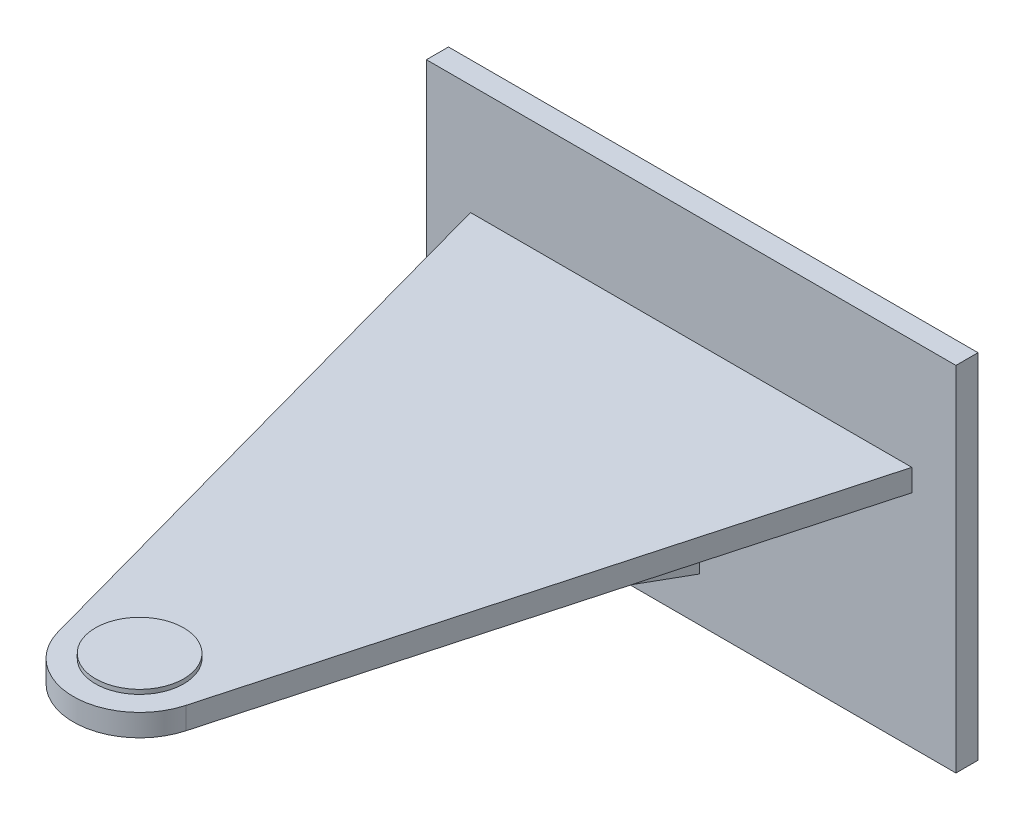
SolidWorks part; units mm, degrees
ref_plane "Frontal" through (0, 0, 0) normal (0, 0, 1) x (1, 0, 0)
ref_plane "Horizontal" through (0, 0, 0) normal (0, 1, 0) x (1, 0, 0)
ref_plane "Profile" through (0, 0, 0) normal (1, 0, 0) x (0, 0, -1)
sketch "Sketch1" plane through (0, 0, 0) normal (0, 0, 1) x (1, 0, 0)
  line L0 (-76.2, 50.8) -> (76.2, -50.8) construction
  line L1 (-76.2, 50.8) -> (76.2, 50.8)
  line L2 (-76.2, 50.8) -> (-76.2, -50.8)
  line L3 (-76.2, -50.8) -> (76.2, -50.8)
  line L4 (76.2, 50.8) -> (76.2, -50.8)
  dimension "D1" = 152.4
  dimension "D2" = 101.6
extrude "Extrude1" add sketch "Sketch1" along normal blind 6.35
ref_plane "Plane1" through (0, 19.05, 0) normal (0, 1, 0) x (-1, 0, 0)
sketch "Sketch3" plane through (0, 19.05, 0) normal (0, 1, 0) x (-1, 0, 0)
  line L0 (0, 0) -> (0, 69.344) construction
  line L1 (63.5, 6.35) -> (18.3656, 170.1603)
  line L2 (-63.5, 6.35) -> (-18.3656, 170.1603)
  line L3 (-76.2, 6.35) -> (76.2, 6.35) construction
  line L4 (63.5, 6.35) -> (-63.5, 6.35)
  arc A0 (18.3656, 170.1603) -> (0, 184.15) centre (0, 165.1) ccw
  arc A1 (-18.3656, 170.1603) -> (0, 184.15) centre (0, 165.1) cw
  dimension "D3" = 19.05
  dimension "D1" = 127
  dimension "D2" = 177.8
extrude "Extrude2" add sketch "Sketch3" against normal blind 6.35
sketch "Sketch4" plane through (0, 19.05, 0) normal (0, 1, 0) x (-1, 0, 0)
  circle A0 centre (0, 165.1) radius 12.7
  dimension "D1" = 25.4
extrude "Extrude3" add sketch "Sketch4" along normal blind 1.27
sketch "Sketch5" plane through (0, 0, 0) normal (1, 0, 0) x (0, 0, -1)
  line L0 (-146.05, 12.7) -> (-6.35, -38.1)
  line L1 (-170.1603, 12.7) -> (-6.35, 12.7) construction
  line L2 (-6.35, -50.8) -> (-6.35, 50.8) construction
  line L3 (-6.35, -38.1) -> (-6.35, 12.7)
  line L4 (-6.35, 12.7) -> (-146.05, 12.7)
  dimension "D1" = 139.7
  dimension "D2" = 50.8
extrude "Extrude4" add sketch "Sketch5" along normal mid plane 4.7625
ref_plane "Plane2" through (25.4, 0, 0) normal (1, 0, 0) x (0, 0, -1)
sketch "Sketch8" plane through (25.4, 0, 0) normal (1, 0, 0) x (0, 0, -1)
  line L0 (-76.2, 12.7) -> (-6.35, -12.7)
  line L5 (-170.1603, 12.7) -> (-6.35, 12.7) construction
  line L6 (-6.35, -50.8) -> (-6.35, 50.8) construction
rib "Rib4" sketch "Sketch8" sketch "Sketch8" thickness 4.7625 extrusion direction parallel to sketch draft on no parameters "D1"=4.7625
